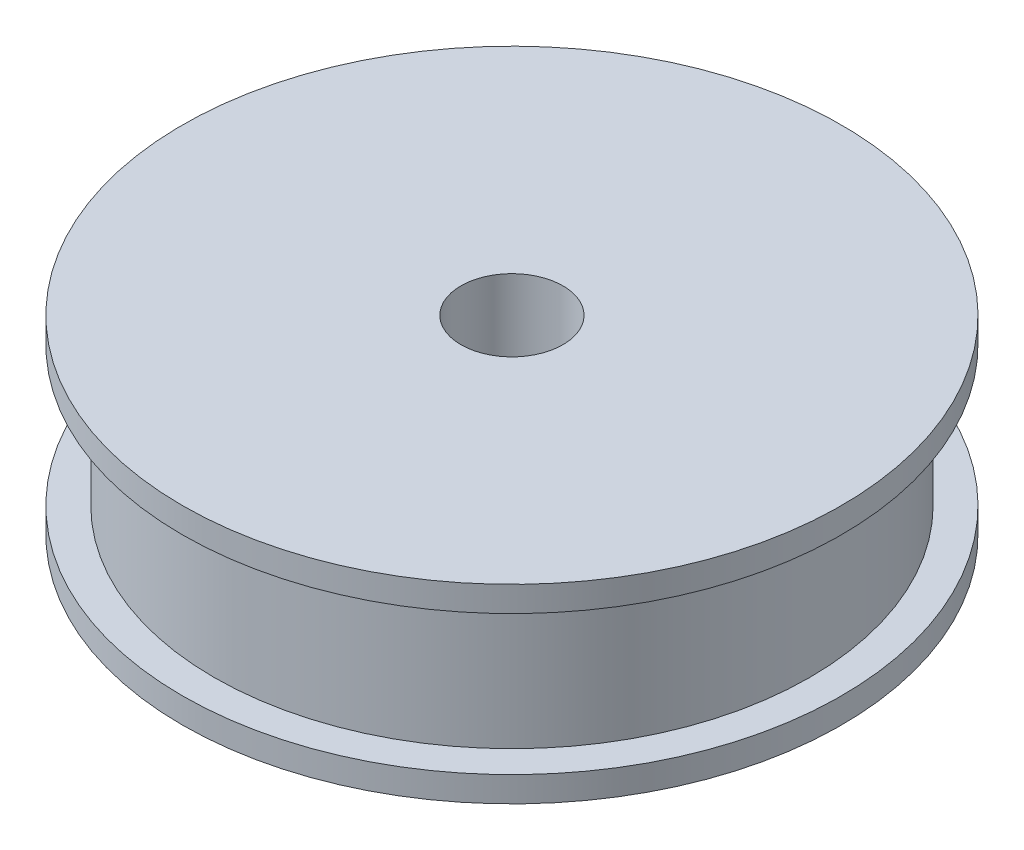
SolidWorks part; units mm, degrees
ref_plane "前视基准面" through (0, 0, 0) normal (0, 0, 1) x (1, 0, 0)
ref_plane "上视基准面" through (0, 0, 0) normal (0, 1, 0) x (1, 0, 0)
ref_plane "右视基准面" through (0, 0, 0) normal (1, 0, 0) x (0, 0, -1)
sketch "草图1" plane through (0, 0, 0) normal (0, 1, 0) x (1, 0, 0)
  circle A0 centre (0, 0) radius 26
  dimension "D1" = 52
extrude "凸台-拉伸1" add sketch "草图1" along normal blind 2
sketch "草图2" plane through (0, 2, 0) normal (0, 1, 0) x (1, 0, 0)
  circle A0 centre (0, 0) radius 23.495
  dimension "D1" = 46.99
extrude "凸台-拉伸2" add sketch "草图2" along normal blind 11
sketch "草图3" plane through (0, 13, 0) normal (0, 1, 0) x (1, 0, 0)
  circle A0 centre (0, 0) radius 26
  dimension "D1" = 52
extrude "凸台-拉伸3" add sketch "草图3" along normal blind 2
sketch "草图4" plane through (0, 15, 0) normal (0, 1, 0) x (1, 0, 0)
  circle A0 centre (0, 0) radius 4.025
  dimension "D1" = 8.05
extrude "切除-拉伸1" cut sketch "草图4" against normal through all
